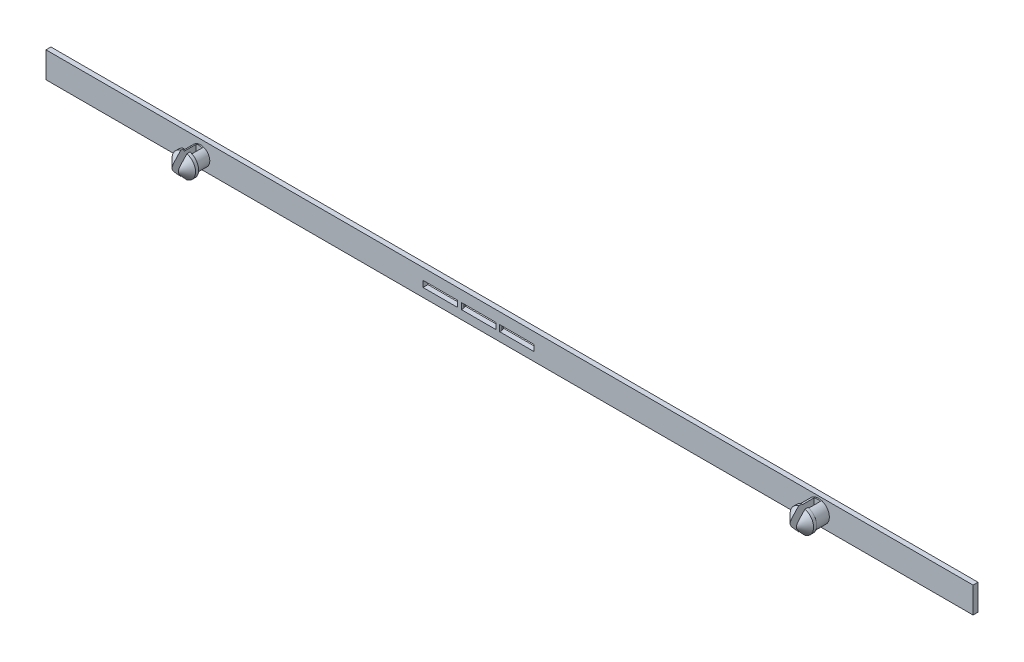
SolidWorks part; units mm, degrees
ref_plane "Přední rovina" through (0, 0, 0) normal (0, 0, 1) x (1, 0, 0)
ref_plane "Horní rovina" through (0, 0, 0) normal (0, 1, 0) x (1, 0, 0)
ref_plane "Pravá rovina" through (0, 0, 0) normal (1, 0, 0) x (0, 0, -1)
sketch "Skica2" plane through (0, 0, 0) normal (0, 0, 1) x (1, 0, 0)
  line L1 (-75, 2.1) -> (75, 2.1)
  line L2 (-75, 2.1) -> (-75, -2.1)
  line L3 (-75, -2.1) -> (75, -2.1)
  line L4 (75, 2.1) -> (75, -2.1)
  line L5 (-75, 2.1) -> (75, -2.1) construction
  line L6 (-75, -2.1) -> (75, 2.1) construction
  line L7 (4, 0.3) -> (-14, 0.3)
  line L8 (4, 0.3) -> (4, -0.7)
  line L9 (4, -0.7) -> (-14, -0.7)
  line L10 (-14, 0.3) -> (-14, -0.7)
  line L11 (4, 0.3) -> (-14, -0.7) construction
  line L12 (4, -0.7) -> (-14, 0.3) construction
  point P0 (0, 0)
  point P5 (-5, -0.2)
  dimension "D1" = 4.2
  dimension "D2" = 150
  dimension "D3" = 1
  dimension "D4" = 18
  dimension "D5" = 61
extrude "Přidat vysunutím2" add sketch "Skica2" along normal blind 0.8
sketch "Skica3" plane through (0, 0, 0.8) normal (0, 0, 1) x (1, 0, 0)
  line L0 (-75, 2.1) -> (-75, -2.1) construction
  line L1 (75, -2.1) -> (75, 2.1) construction
  line L2 (75, 2.1) -> (-75, 2.1) construction
  line L3 (-75, -2.1) -> (75, -2.1) construction
  circle A0 centre (-50, -0.2) radius 1.5
  circle A1 centre (50, 0) radius 1.75
  dimension "D1" = 3
  dimension "D3" = 3.5
  dimension "D2" = 25
  dimension "D4" = 25
  dimension "D5" = 2.3
  dimension "D6" = 1.9
extrude "Přidat vysunutím3" add sketch "Skica3" along normal blind 2.2
sketch "Skica4" plane through (0, 0, 0) normal (0, 0, -1) x (-1, 0, 0)
  line L0 (14, -0.7) -> (-4, -0.7) construction
  line L1 (2.2, 0.3) -> (1.6, 0.3)
  line L2 (2.2, 0.3) -> (2.2, -0.7)
  line L3 (2.2, -0.7) -> (1.6, -0.7)
  line L4 (1.6, 0.3) -> (1.6, -0.7)
  line L5 (2.2, 0.3) -> (1.6, -0.7) construction
  line L6 (2.2, -0.7) -> (1.6, 0.3) construction
  line L7 (-4, -0.7) -> (-4, 0.3) construction
  line L8 (14, 0.3) -> (14, -0.7) construction
  line L9 (7.8, 0.5) -> (8.4, 0.5)
  line L10 (7.8, 0.5) -> (7.8, -0.7)
  line L11 (7.8, -0.7) -> (8.4, -0.7)
  line L12 (8.4, 0.5) -> (8.4, -0.7)
  line L13 (7.8, 0.5) -> (8.4, -0.7) construction
  line L14 (7.8, -0.7) -> (8.4, 0.5) construction
  point P0 (1.9, -0.2)
  point P7 (1.6, -0.2)
  point P10 (8.1, -0.1)
  dimension "D1" = 1
  dimension "D2" = 0.6
  dimension "D3" = 5.6
  dimension "D4" = 0.6
  dimension "D5" = 5.6
  dimension "D6" = 5.6
extrude "Přidat vysunutím4" add sketch "Skica4" against normal blind 0.8
chamfer "Zkosení1" distance 0.4 angle 20 4 edges at (-7.8, -0.2, 0) (-8.4, -0.2, 0) (-2.2, -0.2, 0) (-1.6, -0.2, 0)
sketch "Skica5" plane through (0, 0, 3) normal (0, 0, 1) x (1, 0, 0)
  circle A0 centre (-50, -0.2) radius 1.9
  circle A1 centre (50, 0) radius 1.9
  dimension "D1" = 3.8
  dimension "D2" = 3.8
extrude "Přidat vysunutím5" add sketch "Skica5" along normal blind 2
chamfer "Zkosení2" distance 1.5 angle 45 2 edges at (51.9, 0, 5) (-48.1, -0.2, 5)
sketch "Skica7" plane through (0, 0, 5) normal (0, 0, 1) x (1, 0, 0)
  line L1 (-49.5, 2.3) -> (-50.5, 2.3)
  line L2 (-49.5, 2.3) -> (-49.5, -2.7)
  line L3 (-49.5, -2.7) -> (-50.5, -2.7)
  line L4 (-50.5, 2.3) -> (-50.5, -2.7)
  line L5 (-49.5, 2.3) -> (-50.5, -2.7) construction
  line L6 (-49.5, -2.7) -> (-50.5, 2.3) construction
  line L7 (49.5, 2.5) -> (50.5, 2.5)
  line L8 (49.5, 2.5) -> (49.5, -2.5)
  line L9 (49.5, -2.5) -> (50.5, -2.5)
  line L10 (50.5, 2.5) -> (50.5, -2.5)
  line L11 (49.5, 2.5) -> (50.5, -2.5) construction
  line L12 (49.5, -2.5) -> (50.5, 2.5) construction
  point P0 (-50, -0.2)
  point P5 (50, 0)
  dimension "D1" = 5
  dimension "D2" = 1
  dimension "D3" = 5
  dimension "D4" = 1
extrude "Odebrat vysunutím1" cut sketch "Skica7" against normal blind 4
equation "\"1.5.000mm\"=10"
